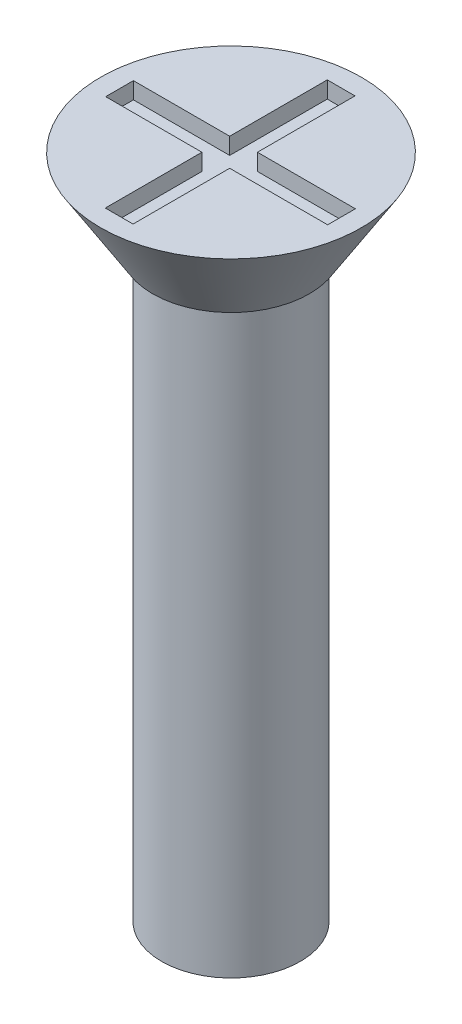
SolidWorks part; units mm, degrees
material "AISI 304"
ref_plane "Front" through (0, 0, 0) normal (0, 0, 1) x (1, 0, 0)
ref_plane "Top" through (0, 0, 0) normal (0, 1, 0) x (1, 0, 0)
ref_plane "Right" through (0, 0, 0) normal (1, 0, 0) x (0, 0, -1)
sketch "Sketch1" plane through (0, 0, 0) normal (0, 1, 0) x (1, 0, 0)
  circle A0 centre (0, 0) radius 1.25
  dimension "D1" = 2.5
extrude "Boss-Extrude1" add sketch "Sketch1" along normal blind 12
sketch "Sketch2" plane through (0, 12, 0) normal (0, 1, 0) x (1, 0, 0)
  circle A0 centre (0, 0) radius 2.35
  dimension "D1" = 4.7
extrude "Boss-Extrude2" add sketch "Sketch2" against normal blind 1.5 draft 32
sketch "Sketch3" plane through (0, 12, 0) normal (0, 1, 0) x (1, 0, 0)
  line L1 (-2, 0.2416) -> (2, 0.2416)
  line L2 (-2, 0.2416) -> (-2, -0.2584)
  line L3 (-2, -0.2584) -> (2, -0.2584)
  line L4 (2, 0.2416) -> (2, -0.2584)
  line L5 (-0.2653, 2) -> (0.2347, 2)
  line L6 (-0.2653, 2) -> (-0.2653, -2)
  line L7 (-0.2653, -2) -> (0.2347, -2)
  line L8 (0.2347, 2) -> (0.2347, -2)
  circle A0 centre (0, 0) radius 2.35 construction
  dimension "D1" = 0.5
  dimension "D2" = 0.5
  dimension "D3" = 4
  dimension "D4" = 4
  dimension "D5" = 2
  dimension "D6" = 2
extrude "Cut-Extrude1" cut sketch "Sketch3" against normal blind 0.3 contours L8 L5 L6 L1 | L8 L3 L6 L7 | L6 L1 L2 L3 | L1 L8 L3 L4 | L8 L1 L6 L3
